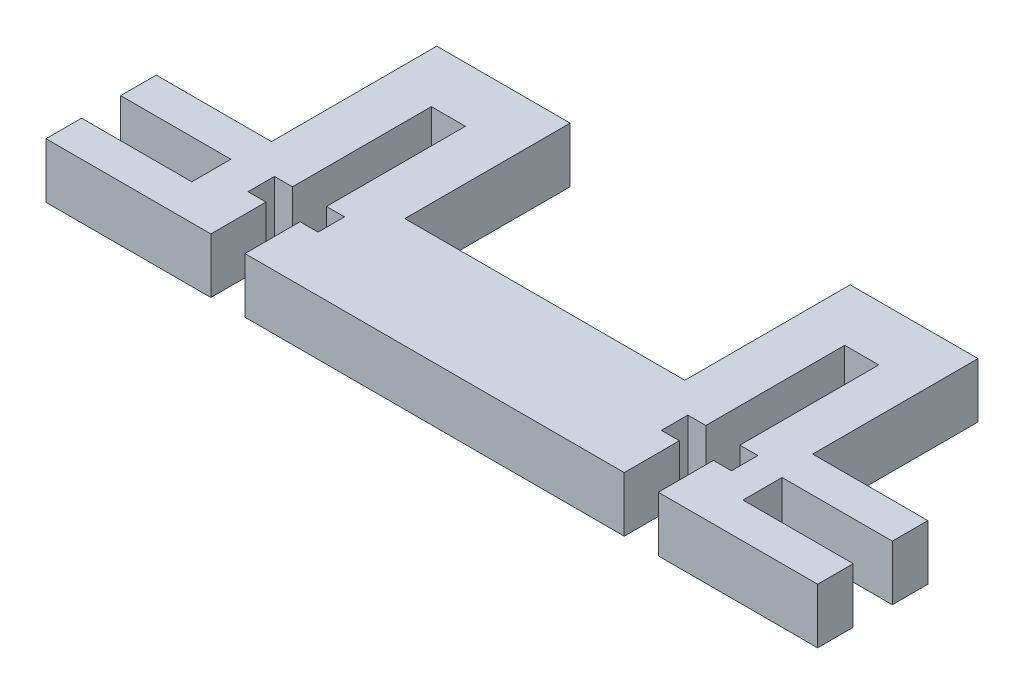
SolidWorks part; units mm, degrees
ref_plane "Front Plane" through (0, 0, 0) normal (0, 0, 1) x (1, 0, 0)
ref_plane "Top Plane" through (0, 0, 0) normal (0, 1, 0) x (1, 0, 0)
ref_plane "Right Plane" through (0, 0, 0) normal (1, 0, 0) x (0, 0, -1)
sketch "Sketch1" plane through (0, 0, 0) normal (0, 1, 0) x (1, 0, 0)
  line L1 (0, 0) -> (88.9, 0)
  line L2 (0, 0) -> (0, -12.7)
  line L3 (0, -12.7) -> (88.9, -12.7)
  line L4 (88.9, 0) -> (88.9, -12.7)
extrude "Boss-Extrude1" add sketch "Sketch1" along normal blind 6.35
sketch "Sketch2" plane through (0, 0, 0) normal (0, 0, -1) x (-1, 0, 0)
  line L0 (-88.9, 6.35) -> (0, 6.35) construction
  line L1 (-75.625, 0.0235) -> (-60.9, 0.0235)
  line L2 (-75.625, 0.0235) -> (-75.625, 6.35)
  line L3 (-75.625, 6.35) -> (-60.9, 6.35)
  line L4 (-60.9, 0.0235) -> (-60.9, 6.35)
  line L5 (-60.9, 6.35) -> (-60.9, 0.0235) construction
  line L6 (-88.9, 0) -> (0, 0) construction
  line L7 (-28.6366, 0) -> (-13.275, 0)
  line L8 (-28.6366, 0) -> (-28.6366, 6.35)
  line L9 (-28.6366, 6.35) -> (-13.275, 6.35)
  line L10 (-13.275, 0) -> (-13.275, 6.35)
  line L11 (-13.275, 6.35) -> (-13.275, 0.0235) construction
extrude "Boss-Extrude2" add sketch "Sketch2" along normal blind 19.05
sketch "Sketch3" plane through (0, 6.35, 0) normal (0, 1, 0) x (1, 0, 0)
  line L0 (0, -6.35) -> (12.7, -6.35) construction
  line L1 (0, 0) -> (0, -12.7) construction
  line L2 (88.9, -6.35) -> (76.2, -6.35) construction
  line L3 (88.9, -12.7) -> (88.9, 0) construction
  line L4 (12.7, -6.35) -> (12.7, -4.1)
  line L5 (12.7, -6.35) -> (12.7, -8.6)
  line L6 (76.2, -6.35) -> (76.2, -4.1)
  line L7 (76.2, -6.35) -> (76.2, -8.6)
  line L8 (12.7, -4.1) -> (0, -4.1)
  line L9 (0, -4.1) -> (0, -8.6)
  line L10 (0, -8.6) -> (12.7, -8.6)
  line L11 (76.2, -4.1) -> (88.9, -4.1)
  line L12 (88.9, -4.1) -> (88.9, -8.6)
  line L13 (88.9, -8.6) -> (76.2, -8.6)
extrude "Cut-Extrude1" cut sketch "Sketch3" against normal through all
sketch "Sketch4" plane through (0, 6.35, 0) normal (0, 1, 0) x (1, 0, 0)
  line L0 (20.9558, 19.05) -> (20.9558, -12.7) construction
  line L1 (13.275, 19.05) -> (28.6366, 19.05) construction
  line L2 (0, -12.7) -> (88.9, -12.7) construction
  line L5 (20.9558, -12.7) -> (22.9183, -12.7)
  line L6 (20.9558, -12.7) -> (18.9933, -12.7)
  line L7 (18.9933, -12.7) -> (18.9933, -6.35)
  line L8 (22.9183, -12.7) -> (22.9183, -6.35)
  line L9 (16.9183, -4.826) -> (20.9558, -4.826) construction
  line L10 (20.9558, -4.826) -> (24.9933, -4.826) construction
  line L11 (16.9183, -6.35) -> (16.9183, -3.302)
  line L12 (18.9933, -6.35) -> (16.9183, -6.35)
  line L13 (22.9183, -6.35) -> (24.9933, -6.35)
  line L14 (16.9183, -3.302) -> (18.9933, -3.302)
  line L15 (24.9933, -6.35) -> (24.9933, -3.302)
  line L16 (24.9933, -3.302) -> (22.9183, -3.302)
  line L17 (22.9183, -3.302) -> (22.9183, 12.7)
  line L18 (22.9183, 12.7) -> (18.9933, 12.7)
  line L19 (18.9933, 12.7) -> (18.9933, -3.302)
  line L24 (44.7683, 0) -> (44.7683, -12.7) construction
  line L38 (60.9, 0) -> (28.6366, 0) construction
  line L39 (68.5808, -4.826) -> (64.5433, -4.826) construction
  line L40 (72.6183, -4.826) -> (68.5808, -4.826) construction
  line L41 (70.5433, 12.7) -> (70.5433, -3.302)
  line L42 (66.6183, 12.7) -> (70.5433, 12.7)
  line L43 (66.6183, -3.302) -> (66.6183, 12.7)
  line L44 (64.5433, -3.302) -> (66.6183, -3.302)
  line L45 (64.5433, -6.35) -> (64.5433, -3.302)
  line L46 (72.6183, -3.302) -> (70.5433, -3.302)
  line L47 (66.6183, -6.35) -> (64.5433, -6.35)
  line L48 (70.5433, -6.35) -> (72.6183, -6.35)
  line L49 (72.6183, -6.35) -> (72.6183, -3.302)
  line L50 (66.6183, -12.7) -> (66.6183, -6.35)
  line L51 (70.5433, -12.7) -> (70.5433, -6.35)
  line L52 (68.5808, -12.7) -> (70.5433, -12.7)
  line L53 (68.5808, -12.7) -> (66.6183, -12.7)
extrude "Cut-Extrude2" cut sketch "Sketch4" against normal through all
